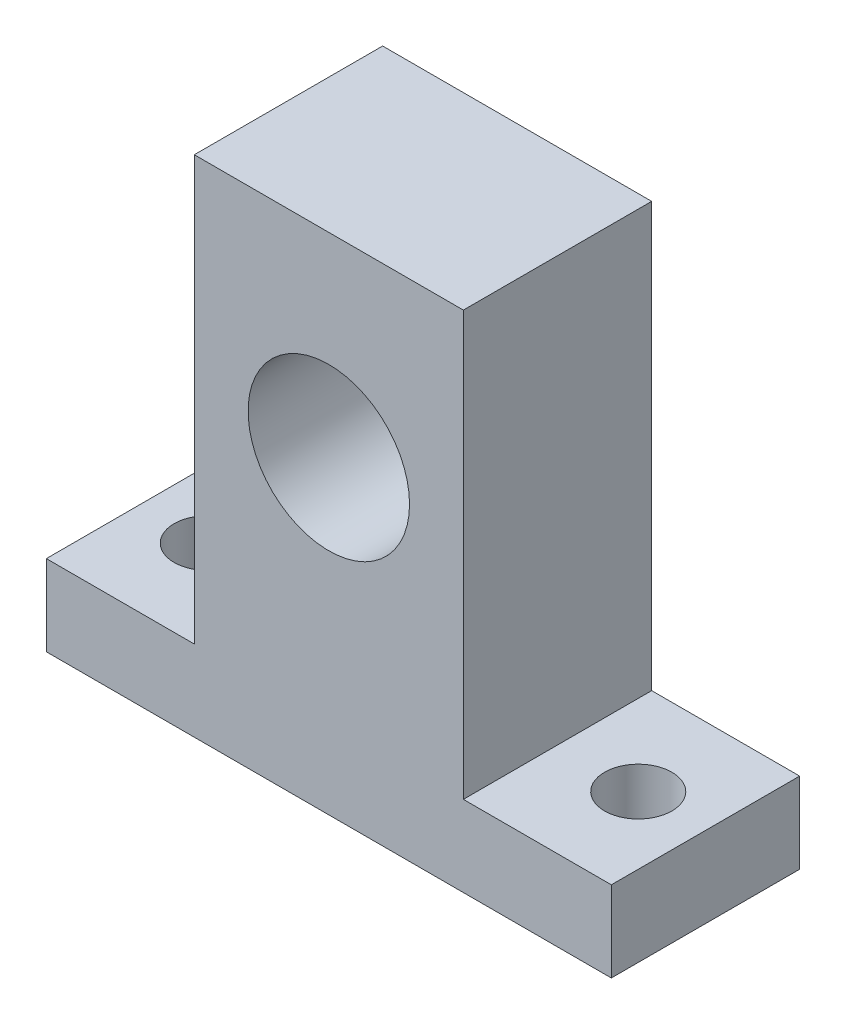
SolidWorks part; units mm, degrees
ref_plane "Front Plane" through (0, 0, 0) normal (0, 0, 1) x (1, 0, 0)
ref_plane "Top Plane" through (0, 0, 0) normal (0, 1, 0) x (1, 0, 0)
ref_plane "Right Plane" through (0, 0, 0) normal (1, 0, 0) x (0, 0, -1)
sketch "Sketch1" plane through (0, 0, 0) normal (0, 0, 1) x (1, 0, 0)
  line L0 (0, 0) -> (0, 6)
  line L1 (0, 6) -> (11, 6)
  line L2 (11, 6) -> (11, 37.5)
  line L3 (11, 37.5) -> (31, 37.5)
  line L4 (31, 37.5) -> (31, 6)
  line L5 (31, 6) -> (42, 6)
  line L6 (42, 6) -> (42, 0)
  line L7 (42, 0) -> (0, 0)
  point P6 (21, 37.5)
  point P10 (21, 0)
  dimension "D1" = 42
  dimension "D2" = 6
  dimension "D3" = 20
  dimension "D4" = 37.5
extrude "Boss-Extrude1" add sketch "Sketch1" against normal blind 14
sketch "Sketch2" plane through (0, 0, 0) normal (0, -1, 0) x (1, 0, 0)
  line L0 (21, 0) -> (21, -14) construction
  line L1 (0, 0) -> (42, 0) construction
  line L2 (0, -14) -> (42, -14) construction
  line L3 (0, -14) -> (0, 0) construction
  circle A0 centre (5, -7) radius 2.5
  circle A1 centre (37, -7) radius 2.5
  point P10 (0, -7)
  dimension "D1" = 5
  dimension "D2" = 32
extrude "Cut-Extrude1" cut sketch "Sketch2" against normal up to next
sketch "Sketch3" plane through (0, 0, 0) normal (0, 0, 1) x (1, 0, 0)
  line L0 (21, 37.5) -> (21, 0) construction
  line L1 (31, 37.5) -> (11, 37.5) construction
  line L2 (0, 0) -> (42, 0) construction
  circle A0 centre (21, 23) radius 6
  dimension "D2" = 12
  dimension "D1" = 23
extrude "Cut-Extrude2" cut sketch "Sketch3" against normal up to next
